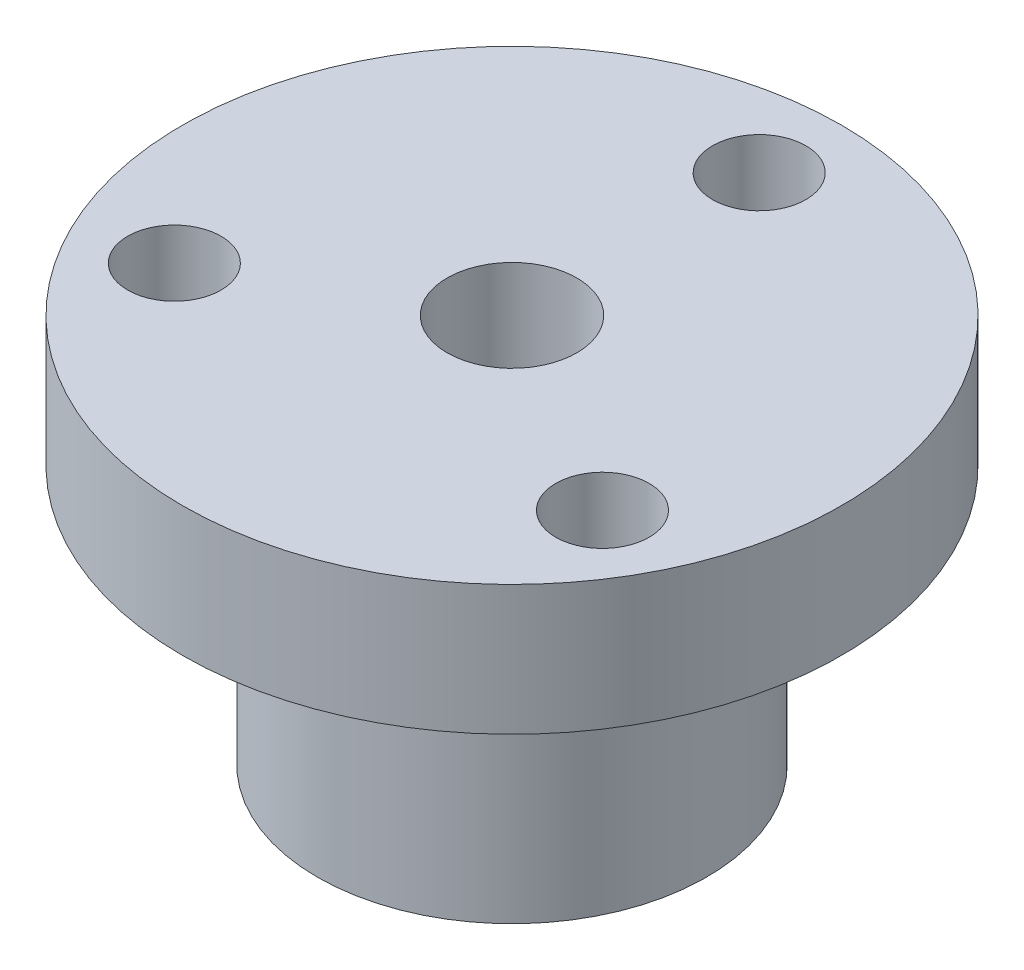
SolidWorks part; units mm, degrees
material "Polybutadiene (PB)"
ref_plane "Front Plane" through (0, 0, 0) normal (0, 0, 1) x (1, 0, 0)
ref_plane "Top Plane" through (0, 0, 0) normal (0, 1, 0) x (1, 0, 0)
ref_plane "Right Plane" through (0, 0, 0) normal (1, 0, 0) x (0, 0, -1)
sketch "Sketch1" plane through (0, 0, 0) normal (0, 1, 0) x (1, 0, 0)
  circle A0 centre (0, 0) radius 7.5
  circle A1 centre (0, 0) radius 2.5
  dimension "D1" = 15
  dimension "D2" = 5
extrude "Boss-Extrude1" add sketch "Sketch1" along normal blind 10
sketch "Sketch2" plane through (0, 10, 0) normal (0, 1, 0) x (-1, 0, 0)
  circle A0 centre (0, 0) radius 2.5
  circle A1 centre (0, 0) radius 12.7
  dimension "D1" = 25.4
  dimension "D2" = 5
extrude "Boss-Extrude2" add sketch "Sketch2" along normal blind 5
sketch "Sketch3" plane through (0, 15, 0) normal (0, 1, 0) x (-1, 0, 0)
  circle A0 centre (0, 0) radius 9.525
  circle A1 centre (0, -9.525) radius 1.8
  circle A2 centre (-8.2489, 4.7625) radius 1.8
  circle A3 centre (0, 0) radius 9.525
  circle A4 centre (8.2489, 4.7625) radius 1.8
  circle A5 centre (0, 0) radius 9.525
  dimension "D1" = 19.05
  dimension "D2" = 3.6
  dimension "D3" = 3
extrude "Cut-Extrude1" cut sketch "Sketch3" against normal through all contours A0 A1 | A0 A1 | A3 A4 | A3 A4 | A0 A2 | A0 A2
